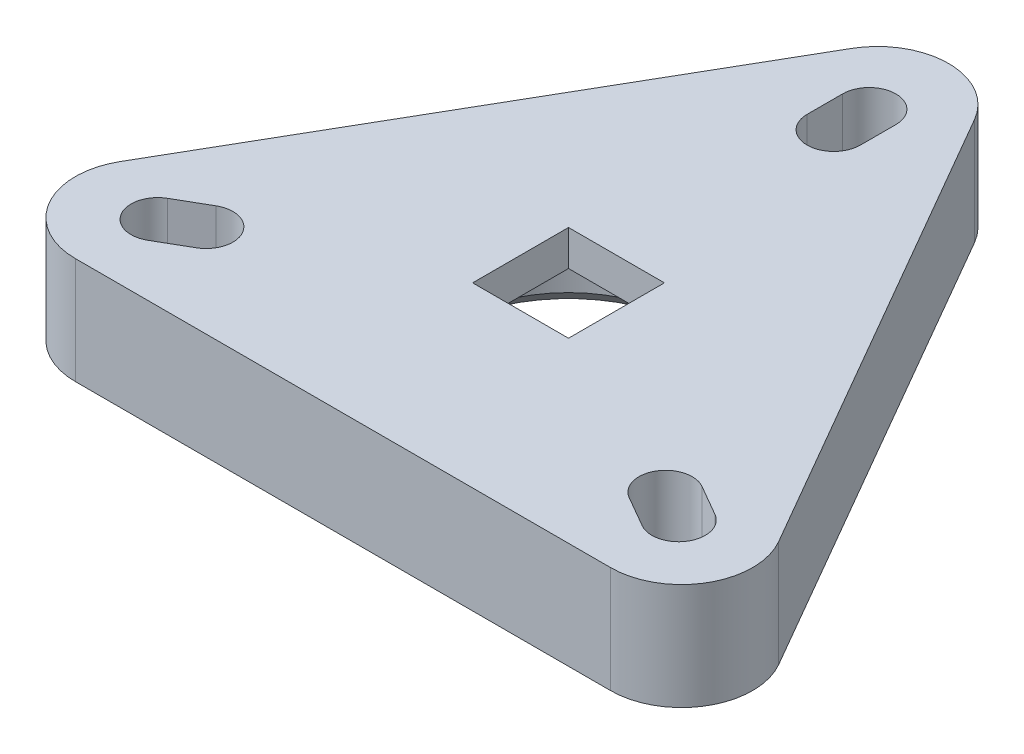
SolidWorks part; units mm, degrees
ref_plane "Front Plane" through (0, 0, 0) normal (0, 0, 1) x (1, 0, 0)
ref_plane "Top Plane" through (0, 0, 0) normal (0, 1, 0) x (1, 0, 0)
ref_plane "Right Plane" through (0, 0, 0) normal (1, 0, 0) x (0, 0, -1)
sketch "Sketch1" plane through (0, 0, 0) normal (0, 1, 0) x (1, 0, 0)
  line L0 (-23.5406, -8.5112) -> (-4.3994, 24.6423)
  line L1 (4.3994, 24.6423) -> (23.5406, -8.5112)
  line L2 (19.1412, -16.1312) -> (-19.1412, -16.1312)
  line L3 (0, 32.2623) -> (0, -16.1312) construction
  line L4 (-27.94, -16.1312) -> (13.97, 8.0656) construction
  line L5 (27.94, -16.1312) -> (-13.97, 8.0656) construction
  line L6 (0, 18.9673) -> (0, 21.5073) construction
  line L7 (0, 20.2373) -> (-17.526, -10.1186) construction
  line L8 (-17.526, -10.1186) -> (17.526, -10.1186) construction
  line L9 (17.526, -10.1186) -> (0, 20.2373) construction
  line L10 (-1.905, 18.9673) -> (-1.905, 21.5073)
  line L11 (1.905, 18.9673) -> (1.905, 21.5073)
  line L12 (-18.6259, -10.7536) -> (-16.4261, -9.4836) construction
  line L13 (-19.5784, -9.1039) -> (-17.3786, -7.8339)
  line L14 (-17.6734, -12.4034) -> (-15.4736, -11.1334)
  line L15 (16.4261, -9.4836) -> (18.6259, -10.7536) construction
  line L16 (17.3786, -7.8339) -> (19.5784, -9.1039)
  line L17 (15.4736, -11.1334) -> (17.6734, -12.4034)
  circle A0 centre (-17.526, -10.1186) radius 1.905
  circle A1 centre (0, 20.2373) radius 1.905
  circle A2 centre (17.526, -10.1186) radius 1.905
  circle A3 centre (0, 0) radius 10.1186 construction
  arc A4 (-1.905, 18.9673) -> (1.905, 18.9673) centre (0, 18.9673) ccw
  arc A5 (1.905, 21.5073) -> (-1.905, 21.5073) centre (0, 21.5073) ccw
  arc A6 (-19.5784, -9.1039) -> (-17.6734, -12.4034) centre (-18.6259, -10.7536) ccw
  arc A7 (-15.4736, -11.1334) -> (-17.3786, -7.8339) centre (-16.4261, -9.4836) ccw
  arc A8 (17.3786, -7.8339) -> (15.4736, -11.1334) centre (16.4261, -9.4836) ccw
  arc A9 (17.6734, -12.4034) -> (19.5784, -9.1039) centre (18.6259, -10.7536) ccw
  arc A10 (23.5406, -8.5112) -> (19.1412, -16.1312) centre (19.1412, -11.0512) cw
  arc A11 (-23.5406, -8.5112) -> (-19.1412, -16.1312) centre (-19.1412, -11.0512) ccw
  arc A12 (-4.3994, 24.6423) -> (4.3994, 24.6423) centre (0, 22.1023) cw
  circle A13 centre (0, 0) radius 3.175
  point P0 (0, 0)
  point P18 (0, 20.2373)
  point P28 (-17.526, -10.1186)
  point P34 (17.526, -10.1186)
  dimension "D1" = 3.81
  dimension "D2" = 35.052
  dimension "D3" = 6.35
  dimension "D5" = 5.08
  dimension "D6" = 6.35
  dimension "D4" = 55.88
extrude "Boss-Extrude1" add sketch "Sketch1" along normal blind 7.62 contours A12 L0 A11 L2 A10 L1 A13 A9 L17 A8 L16 A7 L14 A6 L13 A5 L11 A4 L10
sketch "Sketch2" plane through (0, 0, 0) normal (0, -1, 0) x (1, 0, 0)
  circle A0 centre (0, 0) radius 8.128
  dimension "D1" = 16.256
extrude "Cut-Extrude1" cut sketch "Sketch2" against normal blind 5.08
sketch "Sketch3" plane through (0, 0, 0) normal (0, -1, 0) x (-1, 0, 0)
  line L1 (3.429, 3.429) -> (-3.429, 3.429)
  line L2 (3.429, 3.429) -> (3.429, -3.429)
  line L3 (3.429, -3.429) -> (-3.429, -3.429)
  line L4 (-3.429, 3.429) -> (-3.429, -3.429)
  line L5 (3.429, 3.429) -> (-3.429, -3.429) construction
  line L6 (3.429, -3.429) -> (-3.429, 3.429) construction
  point P0 (0, 0)
  dimension "D1" = 6.858
extrude "Cut-Extrude2" cut sketch "Sketch3" against normal through all
chamfer "Chamfer1" distance 1.27 angle 45 1 edges at (0, 0, -8.128)
